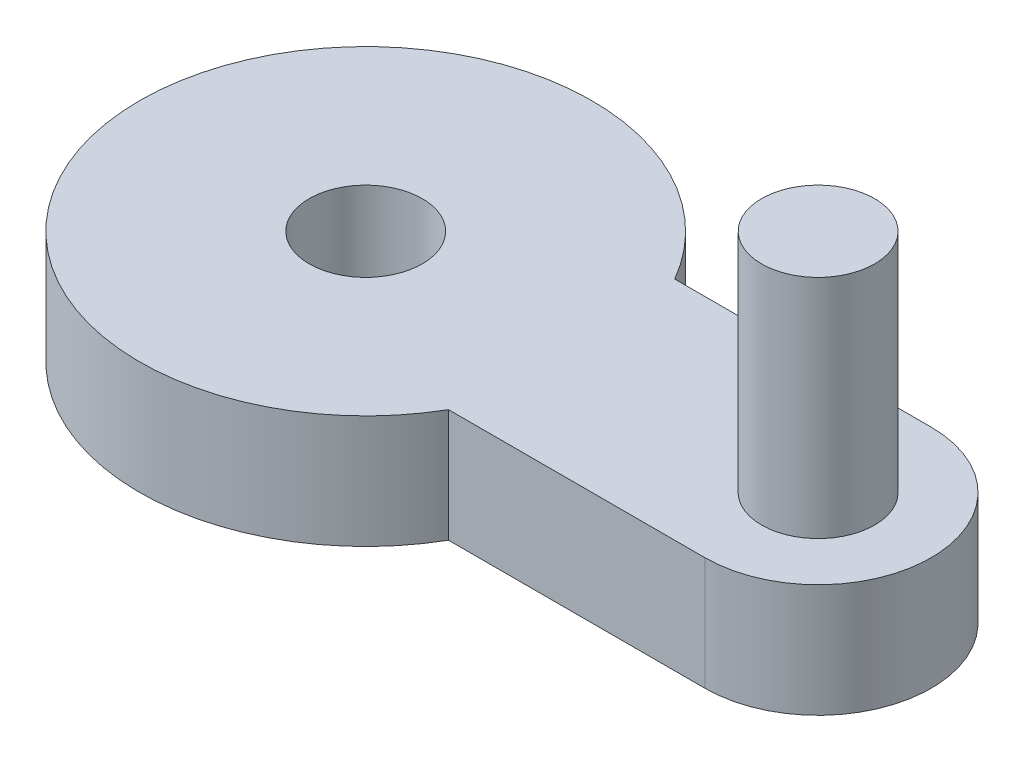
SolidWorks part; units mm, degrees
ref_plane "Front Plane" through (0, 0, 0) normal (0, 0, 1) x (1, 0, 0)
ref_plane "Top Plane" through (0, 0, 0) normal (0, 1, 0) x (1, 0, 0)
ref_plane "Right Plane" through (0, 0, 0) normal (1, 0, 0) x (0, 0, -1)
sketch "Sketch1" plane through (0, 0, 0) normal (0, 1, 0) x (1, 0, 0)
  line L0 (8.6603, 5) -> (20, 5)
  line L1 (20, 5) -> (20, -5) construction
  line L2 (20, -5) -> (8.6603, -5)
  arc A0 (8.6603, 5) -> (8.6603, -5) centre (0, 0) ccw
  arc A1 (20, 5) -> (20, -5) centre (20, 0) cw
  circle A2 centre (0, 0) radius 2.5
  dimension "D1" = 20
  dimension "D4" = 5
  dimension "D2" = 20
  dimension "D3" = 10
extrude "Boss-Extrude1" add sketch "Sketch1" along normal blind 5
sketch "Sketch2" plane through (0, 5, 0) normal (0, 1, 0) x (1, 0, 0)
  line L0 (0, 10) -> (0, -10) construction
  circle A0 centre (20, 0) radius 2.5
  arc A3 (0, 10) -> (0, -10) centre (0, 0) ccw construction
  dimension "D1" = 5
  dimension "D2" = 20
extrude "Boss-Extrude2" add sketch "Sketch2" along normal blind 10
